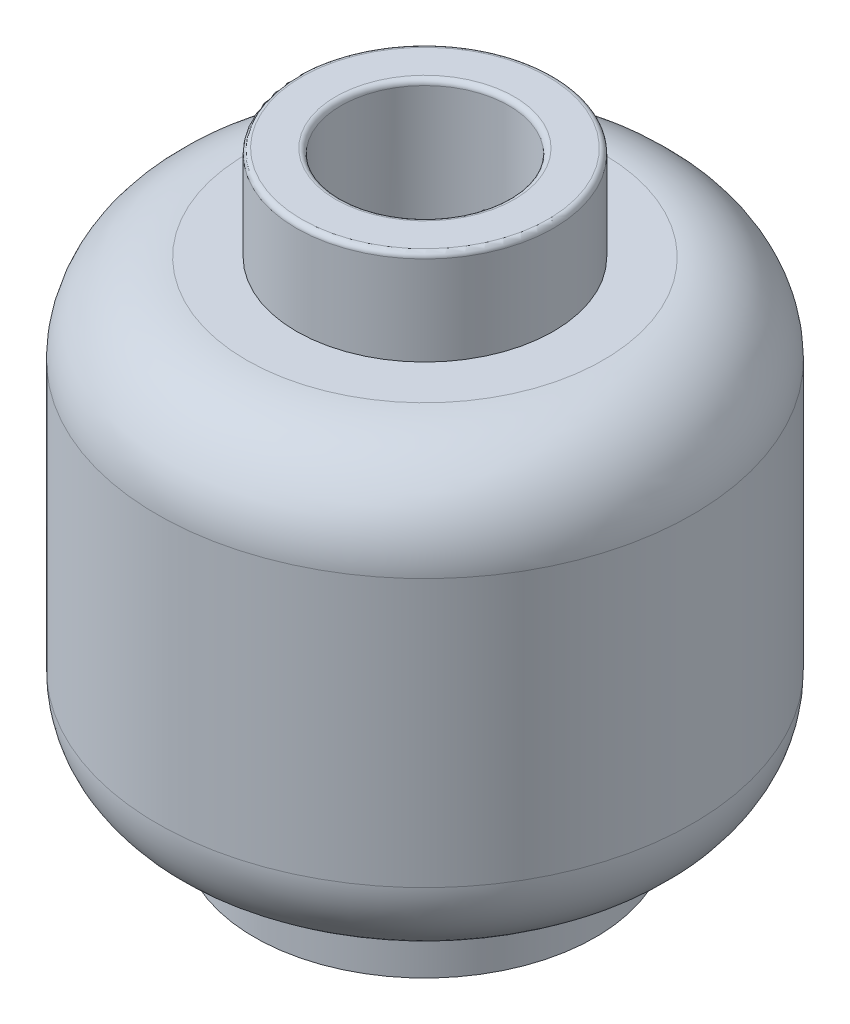
SolidWorks part; units mm, degrees
ref_plane "Alzado" through (0, 0, 0) normal (0, 0, 1) x (1, 0, 0)
ref_plane "Planta" through (0, 0, 0) normal (0, 1, 0) x (1, 0, 0)
ref_plane "Vista lateral" through (0, 0, 0) normal (1, 0, 0) x (0, 0, -1)
sketch "Croquis1" plane through (0, 0, 0) normal (1, 0, 0) x (0, 0, -1)
  line L0 (0, 0) -> (0, 11.4) construction
  line L1 (2.45, 0) -> (3.25, 0)
  line L2 (3.25, 0) -> (3.25, 1.1)
  line L3 (3.25, 1.1) -> (3.4, 1.1)
  line L4 (5.1, 2.8) -> (5.1, 7.9)
  line L5 (3.4, 9.6) -> (2.45, 9.6)
  line L6 (2.45, 9.6) -> (2.45, 11.4)
  line L7 (2.45, 11.4) -> (0, 11.4)
  line L8 (0, 8.5) -> (2.45, 8.5)
  line L9 (2.45, 8.5) -> (2.45, 0)
  line L10 (0, 8.5) -> (0, 11.4)
  arc A0 (5.1, 2.8) -> (3.4, 1.1) centre (3.4, 2.8) cw
  arc A1 (5.1, 7.9) -> (3.4, 9.6) centre (3.4, 7.9) ccw
  point P14 (5.1, 1.1)
  point P17 (5.1, 9.6)
  dimension "D8" = 1.7
  dimension "D1" = 2.45
  dimension "D2" = 0.8
  dimension "D3" = 1.1
  dimension "D4" = 2.9
  dimension "D5" = 1.8
  dimension "D6" = 2.65
  dimension "D7" = 9.6
revolve "Revolución1" add sketch "Croquis1" angle 360 about L0
sketch "Croquis2" plane through (0, 0, 0) normal (0, 0, 1) x (1, 0, 0)
  line L0 (0, 0) -> (0, 13.2773) construction
  line L1 (-6.1882, 5.8) -> (7.1379, 5.8) construction
  line L3 (-6.2406, 3.1) -> (7.0873, 3.1) construction
  line L4 (3.4, 9.6) -> (-3.4, 9.6) construction
  circle A0 centre (1.625, 5.8) radius 0.625
  circle A1 centre (-1.625, 5.8) radius 0.625
  arc A2 (1.4, 3.6422) -> (-1.4, 3.6422) centre (0, 6.85) cw construction
  arc A3 (-1.5, 3.4131) -> (1.5, 3.4131) centre (0, 6.85) ccw
  arc A4 (-1.3, 3.8713) -> (1.3, 3.8713) centre (0, 6.85) ccw
  arc A5 (-1.3, 3.8713) -> (-1.5, 3.4131) centre (-1.4, 3.6422) ccw
  arc A6 (1.5, 3.4131) -> (1.3, 3.8713) centre (1.4, 3.6422) ccw
  point P16 (0, 3.35)
  dimension "D3" = 1.25
  dimension "D5" = 0.25
  dimension "D7" = 3.5
  dimension "D1" = 3.1
  dimension "D2" = 3.8
  dimension "D4" = 3.25
  dimension "D6" = 2.8
split line "Línea de partición1"
sketch "Croquis3" plane through (0, 11.4, 0) normal (0, 1, 0) x (1, 0, 0)
  circle A0 centre (0, 0) radius 1.6
  dimension "D1" = 3.2
extrude "Cortar-Extruir1" cut sketch "Croquis3" against normal blind 2
sketch "Croquis4" plane through (0, 9.4, 0) normal (0, 1, 0) x (1, 0, 0)
  line L0 (0, 0) -> (0, 4.8631) construction
  line L1 (0, 0) -> (-5.6609, -3.2683) construction
  line L2 (-1.547, -0.4082) -> (-0.42, 0.2425)
  line L3 (-0.42, 0.2425) -> (-0.42, 1.5439)
  arc A0 (-0.42, 1.5439) -> (-1.547, -0.4082) centre (0, 0) ccw
  circle A1 centre (0, 0) radius 1.6 construction
  dimension "D1" = 120
  dimension "D2" = 0.42
  dimension "D3" = 0.42
extrude "Cortar-Extruir2" cut sketch "Croquis4" against normal up to next (0.9 mm away)
pattern_circular "MatrizC1" count 3 over 360 about axis through (0, 0, 0) along (0, 1, 0) of "Cortar-Extruir2"
fillet "Redondeo1" radius 0.1 2 edges at (0, 11.4, 1.6) (0, 11.4, -2.45)
